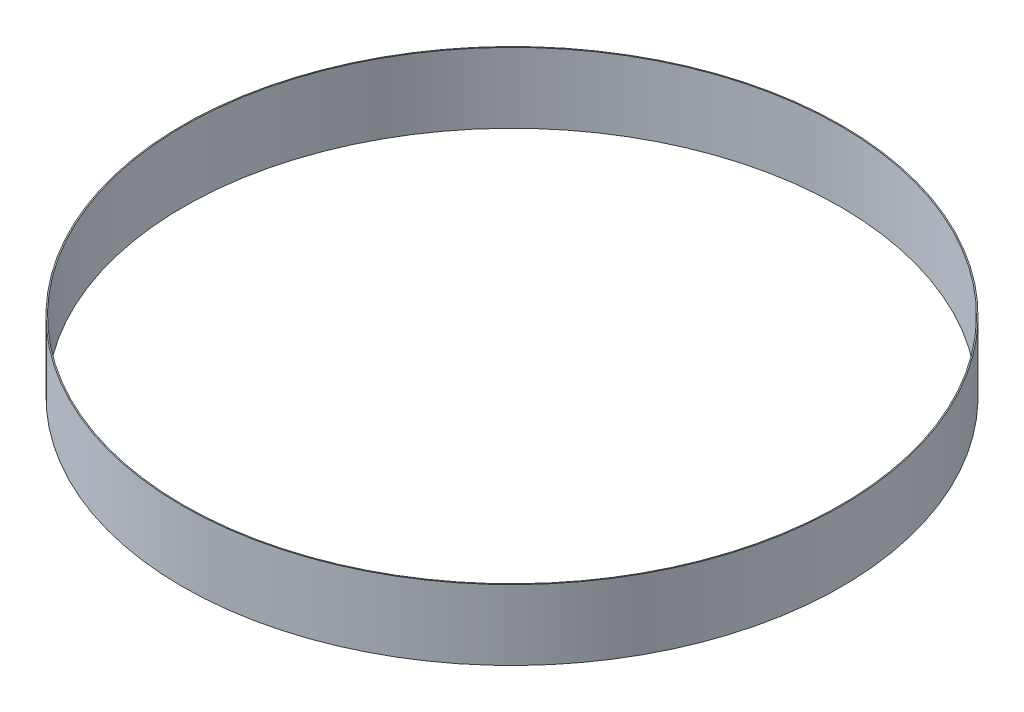
SolidWorks part; units mm, degrees
ref_plane "Front Plane" through (0, 0, 0) normal (0, 0, 1) x (1, 0, 0)
ref_plane "Top Plane" through (0, 0, 0) normal (0, 1, 0) x (1, 0, 0)
ref_plane "Right Plane" through (0, 0, 0) normal (1, 0, 0) x (0, 0, -1)
sketch "Sketch1" plane through (0, 0, 0) normal (0, 1, 0) x (1, 0, 0)
  circle A0 centre (0, 0) radius 150.5
  dimension "D1" = 301
extrude "Boss-Extrude1" add sketch "Sketch1" along normal blind 32 contours A0
sketch "Sketch5" plane through (0, 32, 0) normal (0, 1, 0) x (1, 0, 0)
  circle A0 centre (0, 0) radius 150
  dimension "D1" = 300
extrude "Cut-Extrude1" cut sketch "Sketch5" against normal blind 32 contours A0
